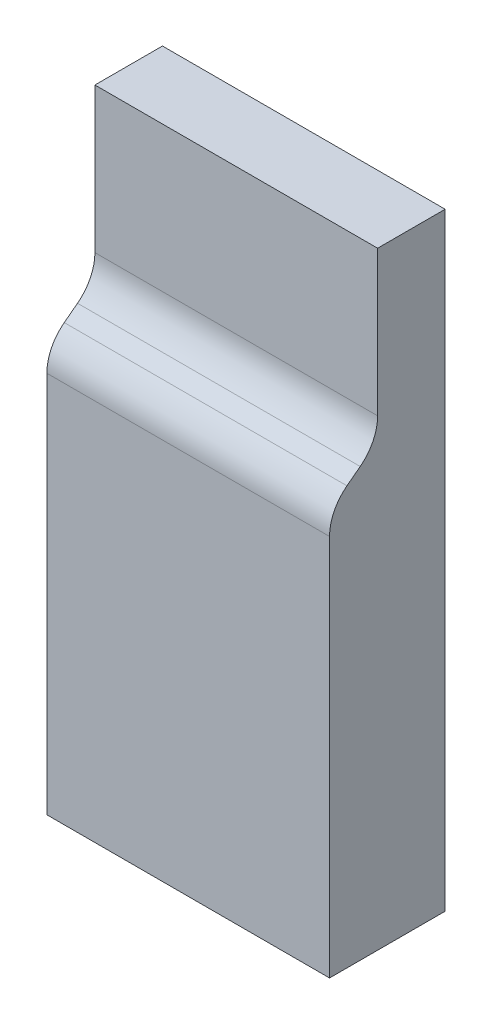
SolidWorks part; units mm, degrees
ref_plane "Front Plane" through (0, 0, 0) normal (0, 0, 1) x (1, 0, 0)
ref_plane "Top Plane" through (0, 0, 0) normal (0, 1, 0) x (1, 0, 0)
ref_plane "Right Plane" through (0, 0, 0) normal (1, 0, 0) x (0, 0, -1)
sketch "Sketch1" plane through (0, 0, 0) normal (0, 0, 1) x (1, 0, 0)
  line L1 (-73.7991, -65.371) -> (-17.7815, -65.371)
  line L2 (-73.7991, -65.371) -> (-73.7991, 55.1059)
  line L3 (-73.7991, 55.1059) -> (-17.7815, 55.1059)
  line L4 (-17.7815, -65.371) -> (-17.7815, 55.1059)
  line L5 (-35.3991, -0.1956) -> (-35.3991, 9.9644) construction
extrude "Boss-Extrude1" add sketch "Sketch1" along normal up to surface (22.9078 mm away)
sketch "Sketch2" plane through (-17.7815, 0, 0) normal (1, 0, 0) x (0, 0, -1)
  line L0 (-17.8201, 18.6199) -> (-16.8317, 19.3736) construction
  line L1 (-18.4706, 18.1237) -> (-17.8201, 18.6199) construction
  line L2 (-19.459, 17.3699) -> (-18.4706, 18.1237) construction
  line L3 (-13.3828, 26.7792) -> (-13.3828, 26.3415) construction
  line L4 (-13.3828, 26.7792) -> (-13.3828, 31.5544) construction
  line L5 (-22.9078, 9.9644) -> (-22.9078, 10.4021) construction
  line L6 (-13.3828, 31.5544) -> (-38.7828, 31.5544) construction
  line L7 (-17.8201, 18.6199) -> (-16.8317, 19.3736)
  line L8 (-18.4706, 18.1237) -> (-17.8201, 18.6199)
  line L9 (-19.459, 17.3699) -> (-18.4706, 18.1237)
  line L10 (-13.3828, 26.7792) -> (-13.3828, 26.3415)
  line L11 (-13.3828, 26.7792) -> (-13.3828, 31.5544)
  line L12 (-22.9078, 9.9644) -> (-22.9078, 10.4021)
  line L13 (-13.3828, 31.5544) -> (-38.7828, 31.5544)
  line L14 (-22.9078, 55.1059) -> (-22.9078, 9.9644)
  line L15 (-22.9078, 55.1059) -> (0, 55.1059) construction
  line L16 (-22.9078, 55.1059) -> (0, 55.1059)
  line L17 (-13.3828, 31.5544) -> (-13.3828, 55.1059)
  arc A0 (-16.8317, 19.3736) -> (-13.4069, 25.6925) centre (-22.1458, 26.3415) ccw construction
  arc A1 (-19.459, 17.3699) -> (-22.8838, 11.0511) centre (-14.1448, 10.4021) ccw construction
  arc A2 (-13.4069, 25.6925) -> (-13.3828, 26.3415) centre (-22.1458, 26.3415) ccw construction
  arc A3 (-22.8838, 11.0511) -> (-22.9078, 10.4021) centre (-14.1448, 10.4021) ccw construction
  arc A4 (-16.8317, 19.3736) -> (-13.4069, 25.6925) centre (-22.1458, 26.3415) ccw
  arc A5 (-19.459, 17.3699) -> (-22.8838, 11.0511) centre (-14.1448, 10.4021) ccw
  arc A6 (-13.4069, 25.6925) -> (-13.3828, 26.3415) centre (-22.1458, 26.3415) ccw
  arc A7 (-22.8838, 11.0511) -> (-22.9078, 10.4021) centre (-14.1448, 10.4021) ccw
  line M1 (0, 55.1059) -> (-22.9078, 55.1059)
  line M2 (-22.9078, 55.1059) -> (-22.9078, -65.371)
extrude "Cut-Extrude1" cut sketch "Sketch2" against normal up to surface (56.0176 mm away) contours A7 A5 L9 L8 L7 A4 A6 L10 L11 M1 M2 | L13 L17 L16 M2
